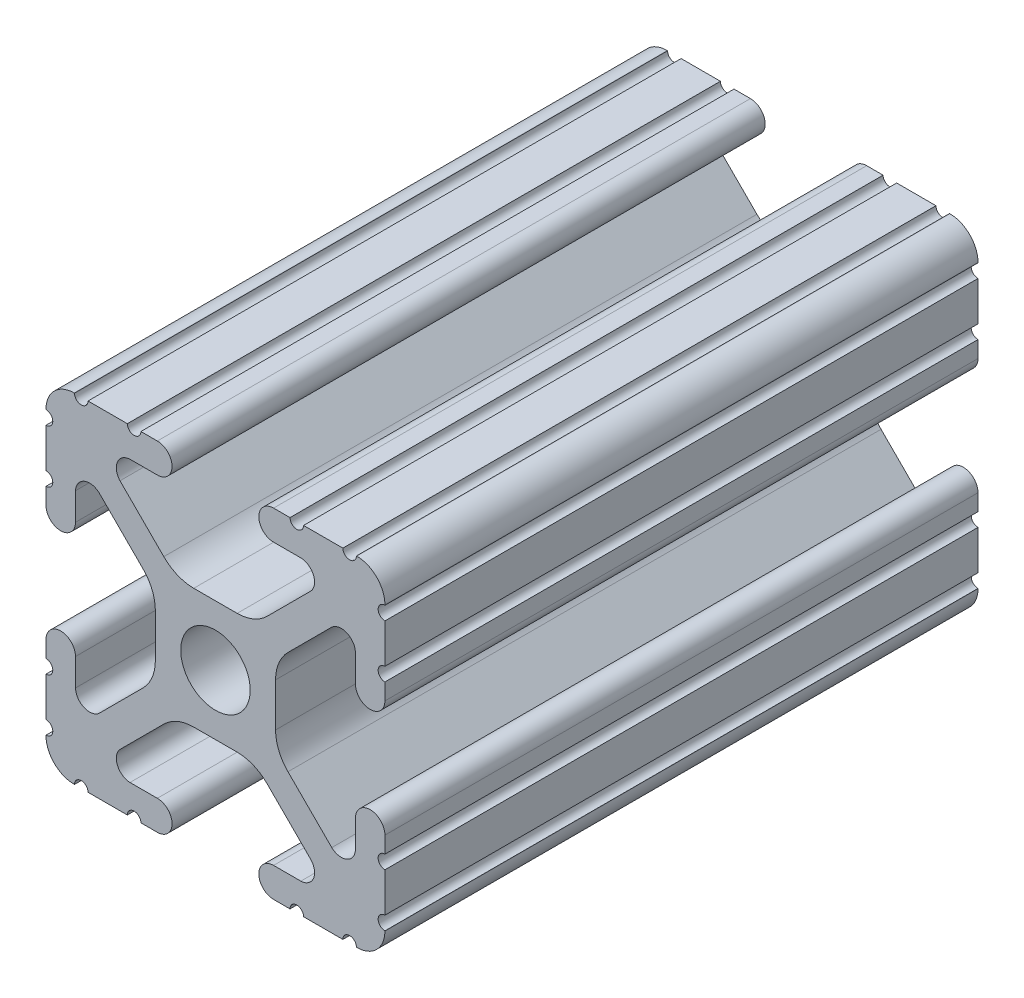
SolidWorks part; units mm, degrees
ref_plane "Front Plane" through (0, 0, 0) normal (0, 0, 1) x (1, 0, 0)
ref_plane "Top Plane" through (0, 0, 0) normal (0, 1, 0) x (1, 0, 0)
ref_plane "Right Plane" through (0, 0, 0) normal (1, 0, 0) x (0, 0, -1)
sketch "Sketch1" plane through (0, 0, 0) normal (0, 0, 1) x (1, 0, 0)
  line L0 (813.039, 579.2904) -> (813.039, 582.2368)
  line L1 (813.039, 583.2528) -> (813.039, 584.4847)
  line L2 (810.8292, 584.4847) -> (810.8292, 582.4359)
  line L3 (809.0573, 581.6856) -> (805.7733, 584.9696)
  line L4 (804.8434, 587.2147) -> (804.8434, 590.4671)
  line L5 (805.7733, 592.7122) -> (809.0571, 595.9959)
  line L6 (810.8292, 595.2394) -> (810.8292, 593.1969)
  line L7 (813.039, 593.1969) -> (813.039, 594.4288)
  line L8 (813.039, 595.4448) -> (813.039, 598.3912)
  line L9 (813.039, 599.4072) -> (813.039, 599.4326)
  line L10 (810.9308, 601.5408) -> (810.9054, 601.5408)
  line L11 (809.8894, 601.5408) -> (806.943, 601.5408)
  line L12 (805.927, 601.5408) -> (804.6951, 601.5408)
  line L13 (804.6951, 599.331) -> (806.7439, 599.331)
  line L14 (807.4942, 597.5592) -> (804.2102, 594.2752)
  line L15 (801.9651, 593.3452) -> (798.7127, 593.3452)
  line L16 (796.4676, 594.2752) -> (793.1839, 597.559)
  line L17 (793.9404, 599.331) -> (795.9829, 599.331)
  line L18 (795.9829, 601.5408) -> (794.751, 601.5408)
  line L19 (793.735, 601.5408) -> (790.7886, 601.5408)
  line L20 (789.7726, 601.5408) -> (789.7472, 601.5408)
  line L21 (787.639, 599.4326) -> (787.639, 599.4072)
  line L22 (787.639, 598.3912) -> (787.639, 595.4448)
  line L23 (787.639, 594.4288) -> (787.639, 593.1969)
  line L24 (789.8488, 593.1969) -> (789.8488, 595.2458)
  line L25 (791.6206, 595.996) -> (794.9046, 592.7121)
  line L26 (795.8346, 590.467) -> (795.8346, 587.2146)
  line L27 (794.9046, 584.9695) -> (791.6208, 581.6858)
  line L28 (789.8488, 582.4423) -> (789.8488, 584.4847)
  line L29 (787.639, 584.4847) -> (787.639, 583.2528)
  line L30 (787.639, 582.2368) -> (787.639, 579.2904)
  line L31 (787.639, 578.2744) -> (787.639, 578.249)
  line L32 (789.7472, 576.1408) -> (789.7726, 576.1408)
  line L33 (790.7886, 576.1408) -> (793.735, 576.1408)
  line L34 (794.751, 576.1408) -> (795.9829, 576.1408)
  line L35 (795.9829, 578.3506) -> (793.934, 578.3506)
  line L36 (793.1838, 580.1225) -> (796.4677, 583.4065)
  line L37 (798.7128, 584.3364) -> (801.9652, 584.3364)
  line L38 (804.2103, 583.4065) -> (807.494, 580.1227)
  line L39 (806.7375, 578.3506) -> (804.6951, 578.3506)
  line L40 (804.6951, 576.1408) -> (805.927, 576.1408)
  line L41 (806.943, 576.1408) -> (809.8894, 576.1408)
  line L42 (810.9054, 576.1408) -> (810.9308, 576.1408)
  line L43 (813.039, 578.249) -> (813.039, 578.2744)
  circle A0 centre (800.339, 588.8408) radius 2.6035
  arc A1 (813.039, 579.2904) -> (813.039, 578.2744) centre (813.039, 578.7824) ccw
  arc A2 (813.039, 583.2528) -> (813.039, 582.2368) centre (813.039, 582.7448) ccw
  arc A3 (813.039, 584.4847) -> (810.8292, 584.4847) centre (811.9341, 584.4847) ccw
  arc A4 (809.0573, 581.6856) -> (810.8292, 582.4359) centre (809.7692, 582.4718) ccw
  arc A5 (804.8434, 587.2147) -> (805.7733, 584.9696) centre (808.0184, 587.2147) ccw
  arc A6 (805.7733, 592.7122) -> (804.8434, 590.4671) centre (808.0184, 590.4671) ccw
  arc A7 (810.8292, 595.2394) -> (809.0571, 595.9959) centre (809.769, 595.2098) ccw
  arc A8 (810.8292, 593.1969) -> (813.039, 593.1969) centre (811.9341, 593.1969) ccw
  arc A9 (813.039, 595.4448) -> (813.039, 594.4288) centre (813.039, 594.9368) ccw
  arc A10 (813.039, 599.4072) -> (813.039, 598.3912) centre (813.039, 598.8992) ccw
  arc A11 (813.039, 599.4326) -> (810.9308, 601.5408) centre (810.9308, 599.4326) ccw
  arc A12 (809.8894, 601.5408) -> (810.9054, 601.5408) centre (810.3974, 601.5408) ccw
  arc A13 (805.927, 601.5408) -> (806.943, 601.5408) centre (806.435, 601.5408) ccw
  arc A14 (804.6951, 601.5408) -> (804.6951, 599.331) centre (804.6951, 600.4359) ccw
  arc A15 (807.4942, 597.5592) -> (806.7439, 599.331) centre (806.708, 598.2711) ccw
  arc A16 (801.9651, 593.3452) -> (804.2102, 594.2752) centre (801.9651, 596.5202) ccw
  arc A17 (796.4676, 594.2752) -> (798.7127, 593.3452) centre (798.7127, 596.5202) ccw
  arc A18 (793.9404, 599.331) -> (793.1839, 597.559) centre (793.97, 598.2709) ccw
  arc A19 (795.9829, 599.331) -> (795.9829, 601.5408) centre (795.9829, 600.4359) ccw
  arc A20 (793.735, 601.5408) -> (794.751, 601.5408) centre (794.243, 601.5408) ccw
  arc A21 (789.7726, 601.5408) -> (790.7886, 601.5408) centre (790.2806, 601.5408) ccw
  arc A22 (789.7472, 601.5408) -> (787.639, 599.4326) centre (789.7472, 599.4326) ccw
  arc A23 (787.639, 598.3912) -> (787.639, 599.4072) centre (787.639, 598.8992) ccw
  arc A24 (787.639, 594.4288) -> (787.639, 595.4448) centre (787.639, 594.9368) ccw
  arc A25 (787.639, 593.1969) -> (789.8488, 593.1969) centre (788.7439, 593.1969) ccw
  arc A26 (791.6206, 595.996) -> (789.8488, 595.2458) centre (790.9087, 595.2099) ccw
  arc A27 (795.8346, 590.467) -> (794.9046, 592.7121) centre (792.6596, 590.467) ccw
  arc A28 (794.9046, 584.9695) -> (795.8346, 587.2146) centre (792.6596, 587.2146) ccw
  arc A29 (789.8488, 582.4423) -> (791.6208, 581.6858) centre (790.9089, 582.4719) ccw
  arc A30 (789.8488, 584.4847) -> (787.639, 584.4847) centre (788.7439, 584.4847) ccw
  arc A31 (787.639, 582.2368) -> (787.639, 583.2528) centre (787.639, 582.7448) ccw
  arc A32 (787.639, 578.2744) -> (787.639, 579.2904) centre (787.639, 578.7824) ccw
  arc A33 (787.639, 578.249) -> (789.7472, 576.1408) centre (789.7472, 578.249) ccw
  arc A34 (790.7886, 576.1408) -> (789.7726, 576.1408) centre (790.2806, 576.1408) ccw
  arc A35 (794.751, 576.1408) -> (793.735, 576.1408) centre (794.243, 576.1408) ccw
  arc A36 (795.9829, 576.1408) -> (795.9829, 578.3506) centre (795.9829, 577.2457) ccw
  arc A37 (793.1838, 580.1225) -> (793.934, 578.3506) centre (793.9699, 579.4106) ccw
  arc A38 (798.7128, 584.3364) -> (796.4677, 583.4065) centre (798.7128, 581.1614) ccw
  arc A39 (804.2103, 583.4065) -> (801.9652, 584.3364) centre (801.9652, 581.1614) ccw
  arc A40 (806.7375, 578.3506) -> (807.494, 580.1227) centre (806.7079, 579.4108) ccw
  arc A41 (804.6951, 578.3506) -> (804.6951, 576.1408) centre (804.6951, 577.2457) ccw
  arc A42 (806.943, 576.1408) -> (805.927, 576.1408) centre (806.435, 576.1408) ccw
  arc A43 (810.9054, 576.1408) -> (809.8894, 576.1408) centre (810.3974, 576.1408) ccw
  arc A44 (810.9308, 576.1408) -> (813.039, 578.249) centre (810.9308, 578.249) ccw
extrude "Extrude1" add sketch "Sketch1" against normal blind 44.45
ref_plane "Plane1" through (806.943, 601.5408, -44.45) normal (0, 0, 1) x (1, 0, 0)
